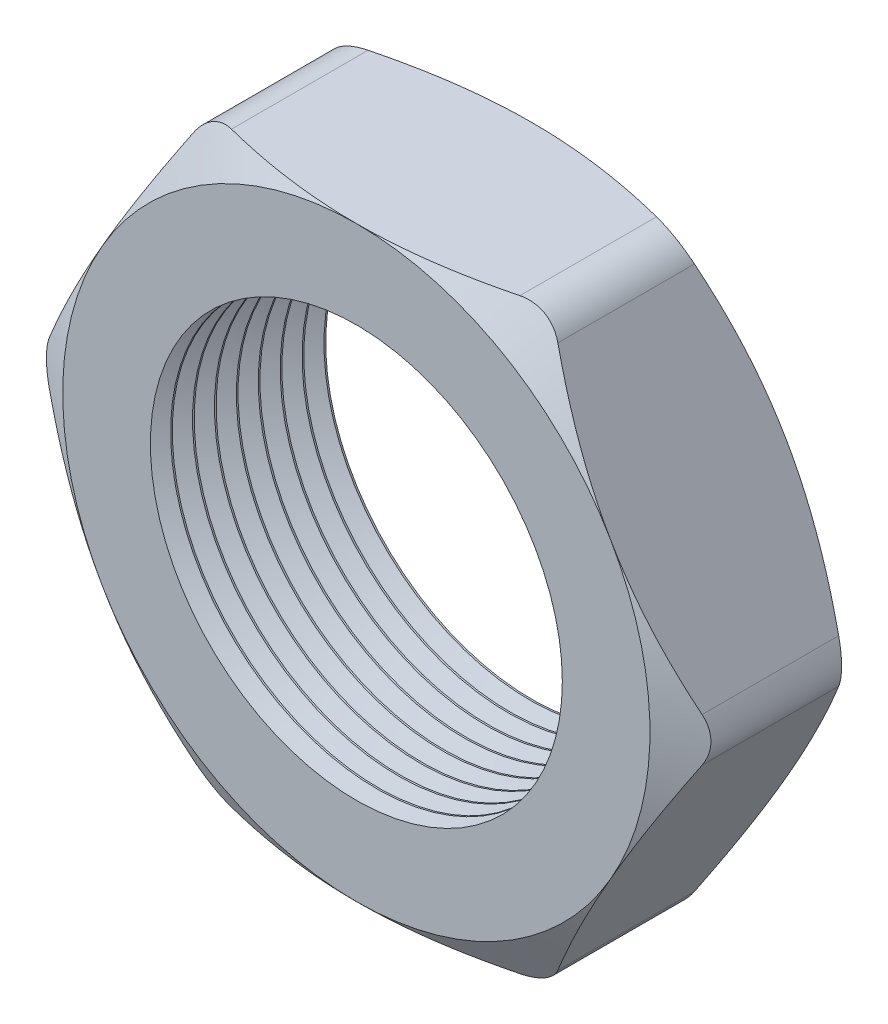
SolidWorks part; units mm, degrees
ref_plane "Front Plane" through (0, 0, 0) normal (0, 0, 1) x (1, 0, 0)
ref_plane "Top Plane" through (0, 0, 0) normal (0, 1, 0) x (1, 0, 0)
ref_plane "Right Plane" through (0, 0, 0) normal (1, 0, 0) x (0, 0, -1)
sketch "Sketch1" plane through (0, 0, 0) normal (0, 0, 1) x (1, 0, 0)
  line L1 (-9.8253, 0) -> (-4.9127, -8.509)
  line L2 (-4.9127, -8.509) -> (4.9127, -8.509)
  line L3 (4.9127, -8.509) -> (9.8253, 0)
  line L4 (9.8253, 0) -> (4.9127, 8.509)
  line L5 (4.9127, 8.509) -> (-4.9127, 8.509)
  line L6 (-4.9127, 8.509) -> (-9.8253, 0)
  circle A0 centre (0, 0) radius 8.509 construction
  circle A1 centre (0, 0) radius 5.969
  dimension "TS" = 11.938
  dimension "H" = 17.018
extrude "Extrude1" add sketch "Sketch1" along normal blind 5.08
sketch "Sketch2" plane through (0, 0, 5.08) normal (0, 0, 1) x (1, 0, 0)
  line L0 (4.9127, 8.509) -> (-4.9127, 8.509) construction
  circle A0 centre (0, 0) radius 8.509
extrude "Cut-Extrude1" cut sketch "Sketch2" against normal through all draft 60 flip side to cut
sketch "Sketch3" plane through (0, 0, 0) normal (0, 0, -1) x (-1, 0, 0)
  line L0 (-4.9127, 8.509) -> (4.9127, 8.509) construction
  circle A0 centre (0, 0) radius 8.509
extrude "Cut-Extrude2" cut sketch "Sketch3" against normal through all draft 60 flip side to cut
fillet "Fillet1" radius 1.27 6 edges at (9.8253, 0, 2.54) (4.9127, -8.509, 2.54) (-4.9127, -8.509, 2.54) (-9.8253, 0, 2.54) (-4.9127, 8.509, 2.54) (4.9127, 8.509, 2.54)
sketch "Sketch4" plane through (0, 0, 0) normal (0, 1, 0) x (1, 0, 0)
  line L0 (-5.969, -5.08) -> (-5.969, -4.4934)
  line L1 (-5.969, 0) -> (-5.969, -5.08) construction
  line L2 (-5.969, -4.4934) -> (-6.477, -4.7867)
  line L3 (-6.477, -4.7867) -> (-5.969, -5.08)
  dimension "D1" = 60
  dimension "D2" = 60
  dimension "D3" = 0.508
revolve "Cut-Revolve1" cut sketch "Sketch4" angle 360 about axis through (0, 0, 0) along (0, 0, 1)
pattern_linear "LPattern1" count 8 spacing 0.635 along (0, 0, -1) of "Cut-Revolve1"
